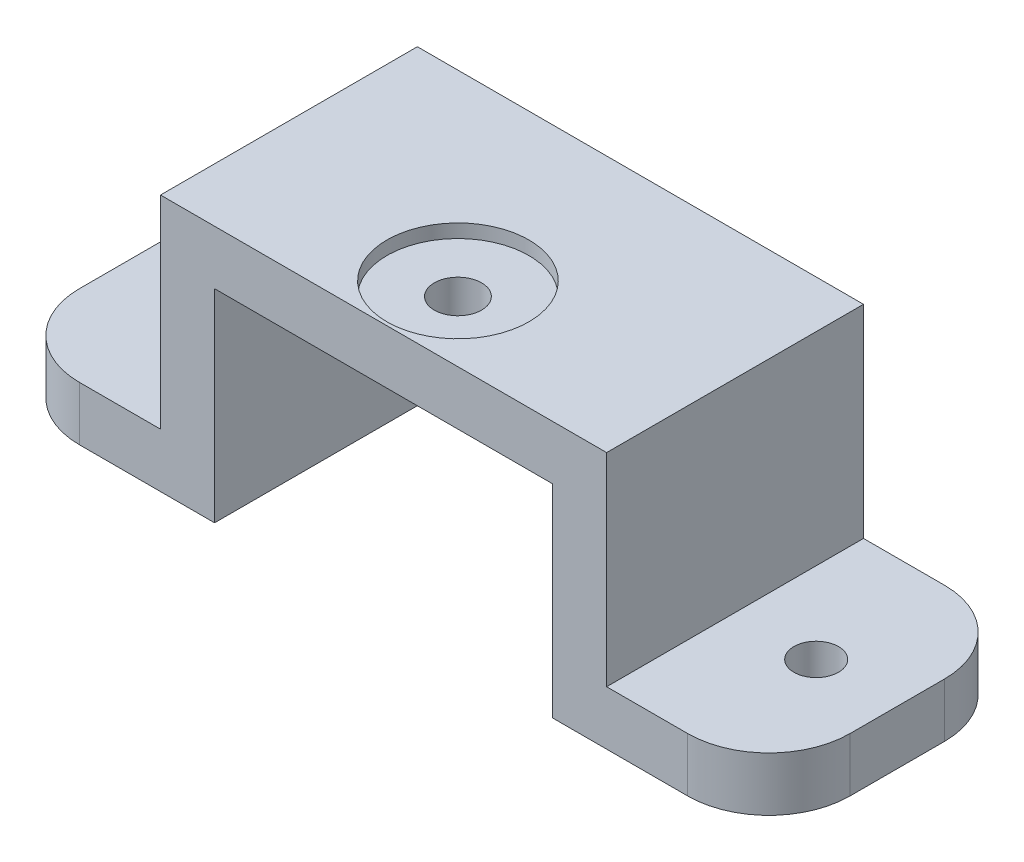
SolidWorks part; units mm, degrees
ref_plane "Plano frontal" through (0, 0, 0) normal (0, 0, 1) x (1, 0, 0)
ref_plane "Plano superior" through (0, 0, 0) normal (0, 1, 0) x (1, 0, 0)
ref_plane "Plano direito" through (0, 0, 0) normal (1, 0, 0) x (0, 0, -1)
sketch "Esboço1" plane through (0, 0, 0) normal (0, 0, 1) x (1, 0, 0)
  line L0 (0, 0) -> (0, 40.1351) construction
  line L1 (12.5, 15) -> (-12.5, 15)
  line L2 (-12.5, 15) -> (-12.5, 0)
  line L3 (-12.5, 0) -> (-28.5, 0)
  line L4 (12.5, 0) -> (28.5, 0)
  line L5 (12.5, 15) -> (12.5, 0)
  line L6 (16.5, 4) -> (28.5, 4)
  line L7 (16.5, 19) -> (16.5, 4)
  line L8 (16.5, 19) -> (-16.5, 19)
  line L9 (-16.5, 19) -> (-16.5, 4)
  line L10 (-16.5, 4) -> (-28.5, 4)
  line L11 (28.5, 0) -> (28.5, 4)
  line L12 (-28.5, 0) -> (-28.5, 4)
  point P10 (0, 15)
  dimension "D1" = 15
  dimension "D2" = 25
  dimension "D3" = 16
  dimension "D4" = 4
extrude "Ressalto-extrusão1" add sketch "Esboço1" along normal blind 19
sketch "Esboço2" plane through (0, 19, 0) normal (0, 1, 0) x (1, 0, 0)
  line L0 (0, 0) -> (0, -19) construction
  line L1 (16.5, 0) -> (-16.5, 0) construction
  line L2 (16.5, -19) -> (-16.5, -19) construction
  line L3 (-28.5, 0) -> (-16.5, 0) construction
  circle A0 centre (0, -13.5) radius 1.75
  circle A1 centre (-22.5, -9.5) radius 1.65
  circle A2 centre (22.5, -9.5) radius 1.65
  point P11 (-22.5, 0)
  point P20 (0, -9.5)
  dimension "D1" = 3.3
  dimension "D2" = 3.5
  dimension "D3" = 4
extrude "Corte-extrusão1" cut sketch "Esboço2" against normal through all both and the other way through all
fillet "Filete1" radius 6 4 edges at (28.5, 2, 0) (28.5, 2, 19) (-28.5, 2, 0) (-28.5, 2, 19)
sketch "Esboço3" plane through (0, 0, 0) normal (0, -1, 0) x (1, 0, 0)
  circle A0 centre (-22.5, 9.5) radius 5
  circle A1 centre (22.5, 9.5) radius 5
  dimension "D1" = 10
extrude "Corte-extrusão2" cut sketch "Esboço3" against normal blind 1
sketch "Esboço4" plane through (0, 19, 0) normal (0, 1, 0) x (1, 0, 0)
  circle A0 centre (0, -13.5) radius 5.25
  dimension "D1" = 10.5
extrude "Corte-extrusão3" cut sketch "Esboço4" against normal blind 1
